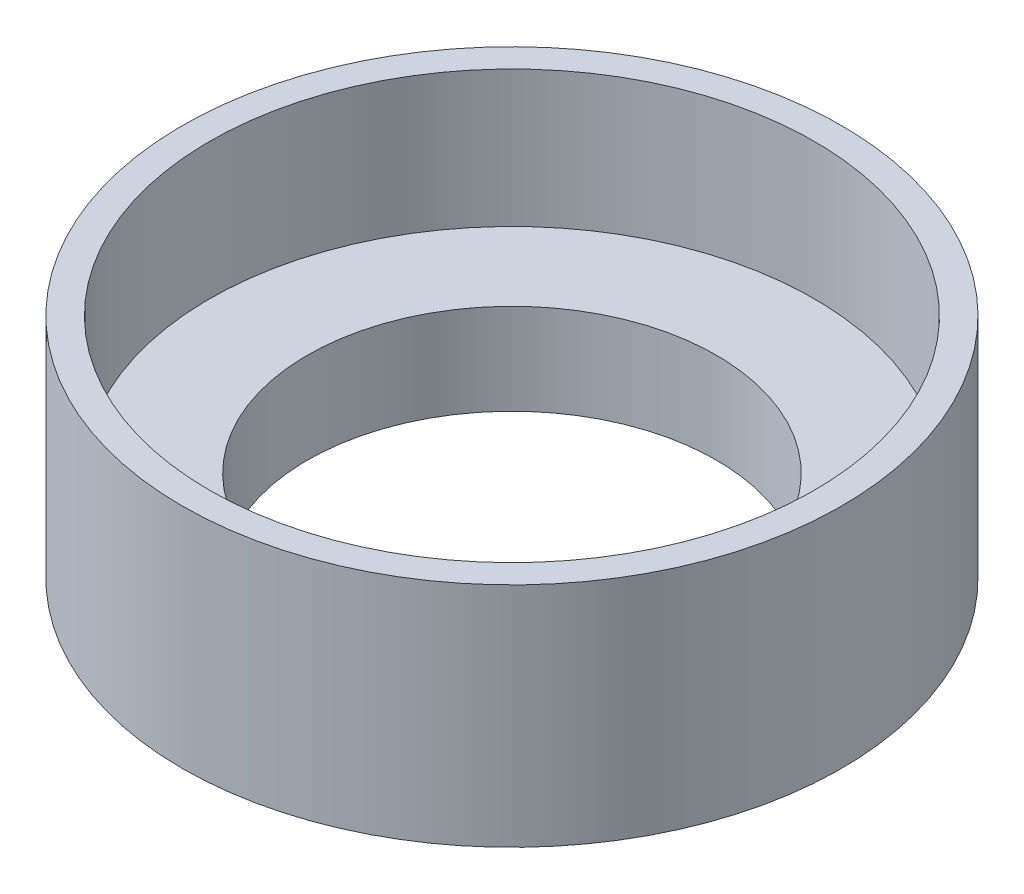
SolidWorks part; units mm, degrees
material "ABS"
ref_plane "Front Plane" through (0, 0, 0) normal (0, 0, 1) x (1, 0, 0)
ref_plane "Top Plane" through (0, 0, 0) normal (0, 1, 0) x (1, 0, 0)
ref_plane "Right Plane" through (0, 0, 0) normal (1, 0, 0) x (0, 0, -1)
sketch "Sketch1" plane through (0, 0, 0) normal (0, 1, 0) x (1, 0, 0)
  circle A0 centre (0, 0) radius 18.415
  dimension "D1" = 36.83
extrude "Boss-Extrude1" add sketch "Sketch1" along normal blind 12.7
sketch "Sketch2" plane through (0, 12.7, 0) normal (0, 1, 0) x (1, 0, 0)
  circle A0 centre (0, 0) radius 16.891
  dimension "D1" = 33.782
extrude "Cut-Extrude1" cut sketch "Sketch2" against normal blind 7.62
sketch "Sketch3" plane through (0, 5.08, 0) normal (0, 1, 0) x (1, 0, 0)
  circle A0 centre (0, 0) radius 11.43
  dimension "D1" = 22.86
extrude "Cut-Extrude2" cut sketch "Sketch3" along normal through all both and the other way through all
